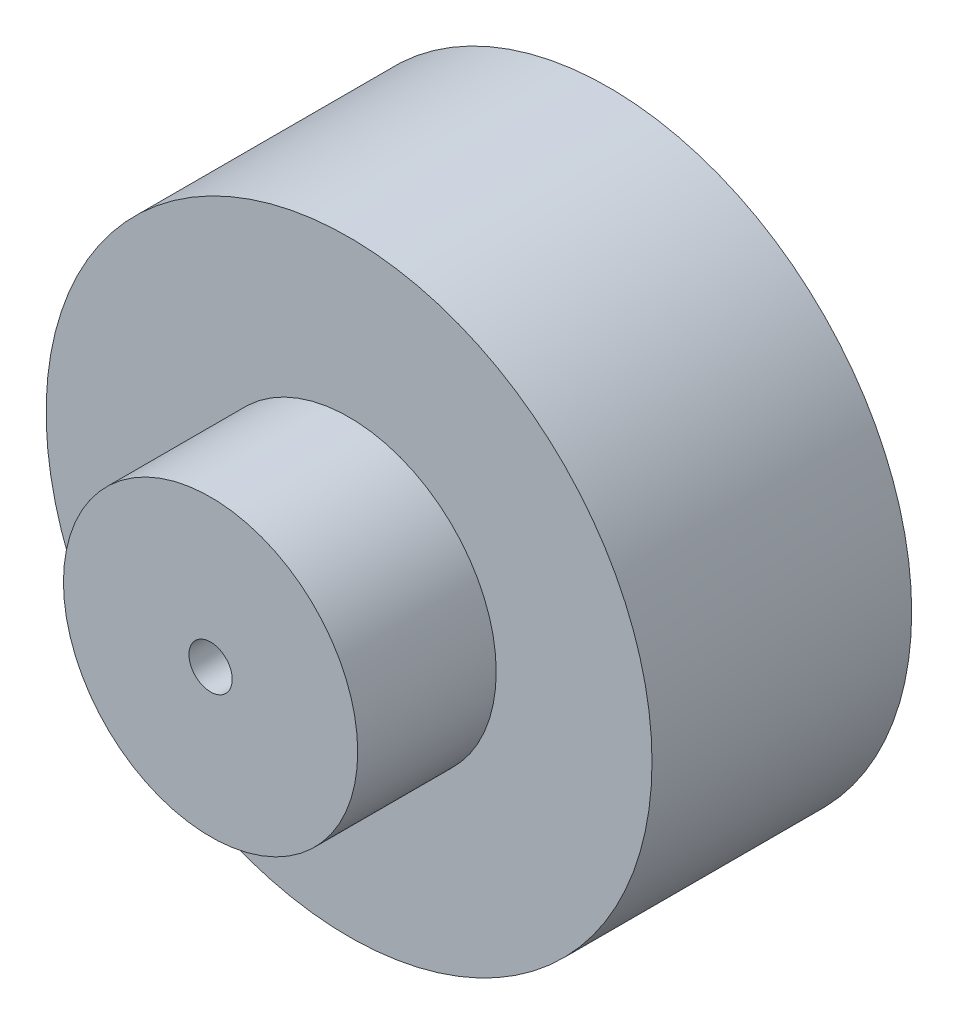
SolidWorks part; units mm, degrees
ref_plane "Front Plane" through (0, 0, 0) normal (0, 0, 1) x (1, 0, 0)
ref_plane "Top Plane" through (0, 0, 0) normal (0, 1, 0) x (1, 0, 0)
ref_plane "Right Plane" through (0, 0, 0) normal (1, 0, 0) x (0, 0, -1)
sketch "Sketch1" plane through (0, 0, 0) normal (0, 0, 1) x (1, 0, 0)
  circle A0 centre (0, 0) radius 17.5
  dimension "D1" = 35
extrude "Boss-Extrude1" add sketch "Sketch1" along normal blind 15
sketch "Sketch2" plane through (0, 0, 15) normal (0, 0, 1) x (1, 0, 0)
  circle A0 centre (0, 0) radius 8.5
  dimension "D1" = 17
extrude "Boss-Extrude2" add sketch "Sketch2" along normal blind 8
sketch "Sketch3" plane through (0, 0, 23) normal (0, 0, 1) x (1, 0, 0)
  circle A0 centre (0, 0) radius 1.25
  dimension "D1" = 2.5
extrude "Cut-Extrude1" cut sketch "Sketch3" against normal blind 20
